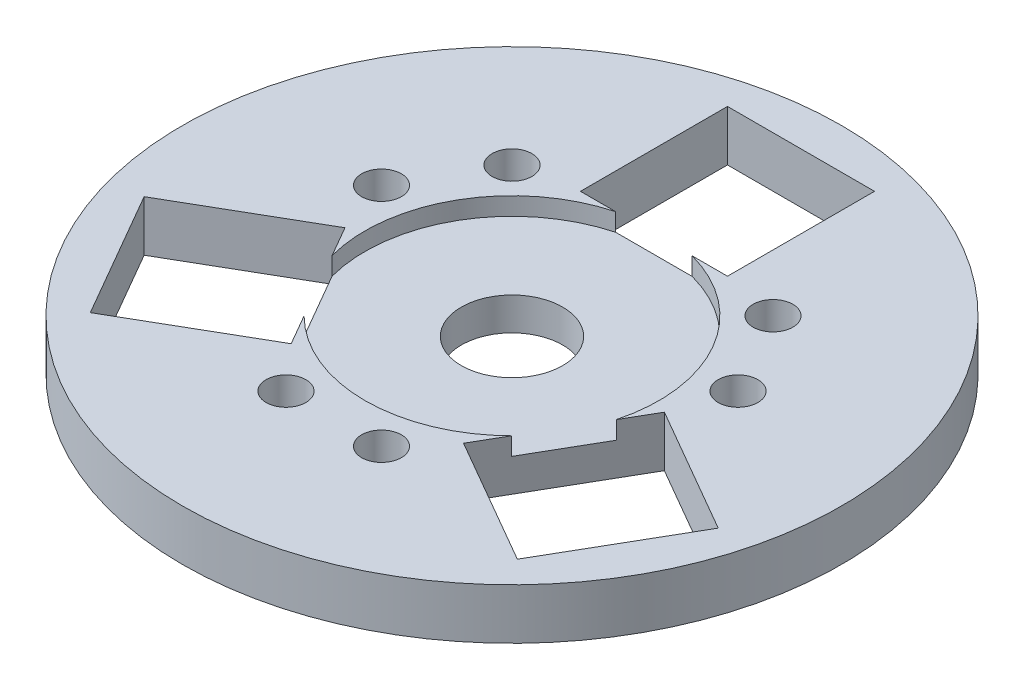
SolidWorks part; units mm, degrees
material "Alum Plate"
ref_plane "Front Plane" through (0, 0, 0) normal (0, 0, 1) x (1, 0, 0)
ref_plane "Top Plane" through (0, 0, 0) normal (0, 1, 0) x (1, 0, 0)
ref_plane "Right Plane" through (0, 0, 0) normal (1, 0, 0) x (0, 0, -1)
other "Bounding Box"
ref_plane "Default Plane" through (-8.9266, -12.7485, 0) normal (-0.1736, 0.9848, 0) x (0.9848, 0.1736, 0)
sketch "Sketch1" plane through (0, 0, 0) normal (0, 1, 0) x (1, 0, 0)
  line L1 (-15.24, 15.24) -> (15.24, 15.24) construction
  line L2 (-15.24, 15.24) -> (-15.24, -15.24) construction
  line L3 (-15.24, -15.24) -> (15.24, -15.24) construction
  line L4 (15.24, 15.24) -> (15.24, -15.24) construction
  line L5 (-15.24, 15.24) -> (15.24, -15.24) construction
  line L6 (-15.24, -15.24) -> (15.24, 15.24) construction
  circle A0 centre (0, 0) radius 44.45
  circle A1 centre (-15.24, -15.24) radius 1.905 construction
  circle A2 centre (-15.24, 15.24) radius 1.905 construction
  circle A3 centre (15.24, 15.24) radius 1.905 construction
  circle A4 centre (15.24, -15.24) radius 1.905 construction
  circle A5 centre (0, 0) radius 6.35
  dimension "D1" = 88.9
  dimension "D3" = 3.81
  dimension "D4" = 12.7
  dimension "D2" = 30.48
extrude "Boss-Extrude1" add sketch "Sketch1" along normal mid plane 6.35
sketch "Sketch4" plane through (0, 3.175, 0) normal (0, 1, 0) x (1, 0, 0)
  circle A0 centre (-15.24, -15.24) radius 1.905 construction
  circle A1 centre (15.24, -15.24) radius 1.905 construction
  circle A2 centre (15.24, 15.24) radius 1.905 construction
  circle A3 centre (-15.24, 15.24) radius 1.905 construction
  circle A4 centre (-15.24, -15.24) radius 1.905
  circle A5 centre (15.24, -15.24) radius 1.905
  circle A6 centre (15.24, 15.24) radius 1.905
  circle A7 centre (-15.24, 15.24) radius 1.905
extrude "Cut-Extrude3" [suppressed] cut sketch "Sketch4" against normal through all
sketch "Sketch2" plane through (0, 3.175, 0) normal (0, 1, 0) x (1, 0, 0)
  line L0 (0, 0) -> (0, 33.601) construction
  line L1 (0, 33.601) -> (-14.2875, 33.601) construction
  line L2 (0, 33.601) -> (14.2875, 33.601) construction
  line L3 (-16.1511, 37.9838) -> (-17.3935, 40.9056) construction
  circle A0 centre (-14.2875, 33.601) radius 2.4892
  circle A1 centre (14.2875, 33.601) radius 2.4892
  circle A2 centre (-14.2875, 33.601) radius 4.7625 construction
  circle A3 centre (14.2875, 33.601) radius 4.7625 construction
  circle A4 centre (0, 0) radius 44.45 construction
  dimension "D1" = 4.9784
  dimension "D2" = 9.525
  dimension "D3" = 28.575
  dimension "D4" = 3.175
extrude "Cut-Extrude1" [suppressed] cut sketch "Sketch2" against normal through all
sketch "Sketch5" plane through (0, 3.175, 0) normal (0, 1, 0) x (1, 0, 0)
  line L0 (0, 0) -> (0, 18.415) construction
  line L1 (-9.2075, 17.78) -> (9.2075, 17.78)
  line L2 (-8.5725, 35.56) -> (8.5725, 35.56) construction
  line L3 (-8.5725, 35.56) -> (-8.5725, 18.415) construction
  line L4 (-8.5725, 18.415) -> (8.5725, 18.415) construction
  line L5 (8.5725, 35.56) -> (8.5725, 18.415) construction
  line L6 (-8.5725, 35.56) -> (8.5725, 18.415) construction
  line L7 (-8.5725, 18.415) -> (8.5725, 35.56) construction
  line L8 (9.2075, 36.195) -> (9.2075, 17.78)
  line L9 (-9.2075, 36.195) -> (9.2075, 36.195)
  line L10 (-9.2075, 36.195) -> (-9.2075, 17.78)
  dimension "D1" = 18.415
  dimension "D2" = 17.145
  dimension "D3" = 0.635
extrude "Cut-Extrude4" cut sketch "Sketch5" against normal through all
pattern_circular "CirPattern1" [suppressed] count 3 over 360
pattern_circular "CirPattern2" count 3 over 360 about axis through (0, 0, 0) along (0, 1, 0) of "Cut-Extrude4"
sketch "Sketch3" plane through (0, 3.175, 0) normal (0, 1, 0) x (1, 0, 0)
  circle A0 centre (0, 0) radius 44.45
  circle A1 centre (0, 0) radius 41.275
  circle A2 centre (0, 0) radius 44.45 construction
  dimension "D1" = 3.175
extrude "Cut-Extrude2" cut sketch "Sketch3" against normal through all
sketch "Sketch6" plane through (0, 3.175, 0) normal (0, 1, 0) x (1, 0, 0)
  circle A0 centre (0, 0) radius 18.415
  dimension "D1" = 36.83
extrude "Cut-Extrude5" cut sketch "Sketch6" against normal offset from surface (2.2352 mm away) 4.1148 up to face at (0, -3.175, 6.35)
sketch "Sketch7" plane through (0, 3.175, 0) normal (0, 1, 0) x (1, 0, 0)
  line L0 (-16.3441, 16.3441) -> (0, 0) construction
  line L1 (0, 0) -> (0, 41.275) construction
  line L2 (0, 0) -> (-22.3264, 5.9823) construction
  line L3 (0, 0) -> (-35.7452, -20.6375) construction
  line L4 (-35.7452, -20.6375) -> (-22.3264, 5.9823) construction
  line L5 (-22.3264, 5.9823) -> (-16.3441, 16.3441) construction
  line L6 (-16.3441, 16.3441) -> (0, 41.275) construction
  line L7 (-20.0017, -0.9161) -> (-35.9495, -10.1236) construction
  circle A0 centre (-16.3441, 16.3441) radius 2.4892
  circle A1 centre (0, 0) radius 41.275 construction
  circle A2 centre (-16.3441, 16.3441) radius 4.7625 construction
  circle A3 centre (-22.3264, 5.9823) radius 2.4892
  dimension "D2" = 4.9784
  dimension "D3" = 9.525
  dimension "D1" = 45
  dimension "D4" = 23.114
extrude "Cut-Extrude6" cut sketch "Sketch7" against normal through all
sketch "Sketch8" plane through (0, 3.175, 0) normal (0, 1, 0) x (1, 0, 0)
  circle A0 centre (-16.3441, 16.3441) radius 4.7625
  dimension "D1" = 9.525
extrude "Cut-Extrude7" [suppressed] cut sketch "Sketch8" against normal up to surface (2.2352 mm away)
pattern_circular "CirPattern3" count 3 over 360 about axis through (0, 0, 0) along (0, 1, 0) of "Cut-Extrude6", "Cut-Extrude7"
